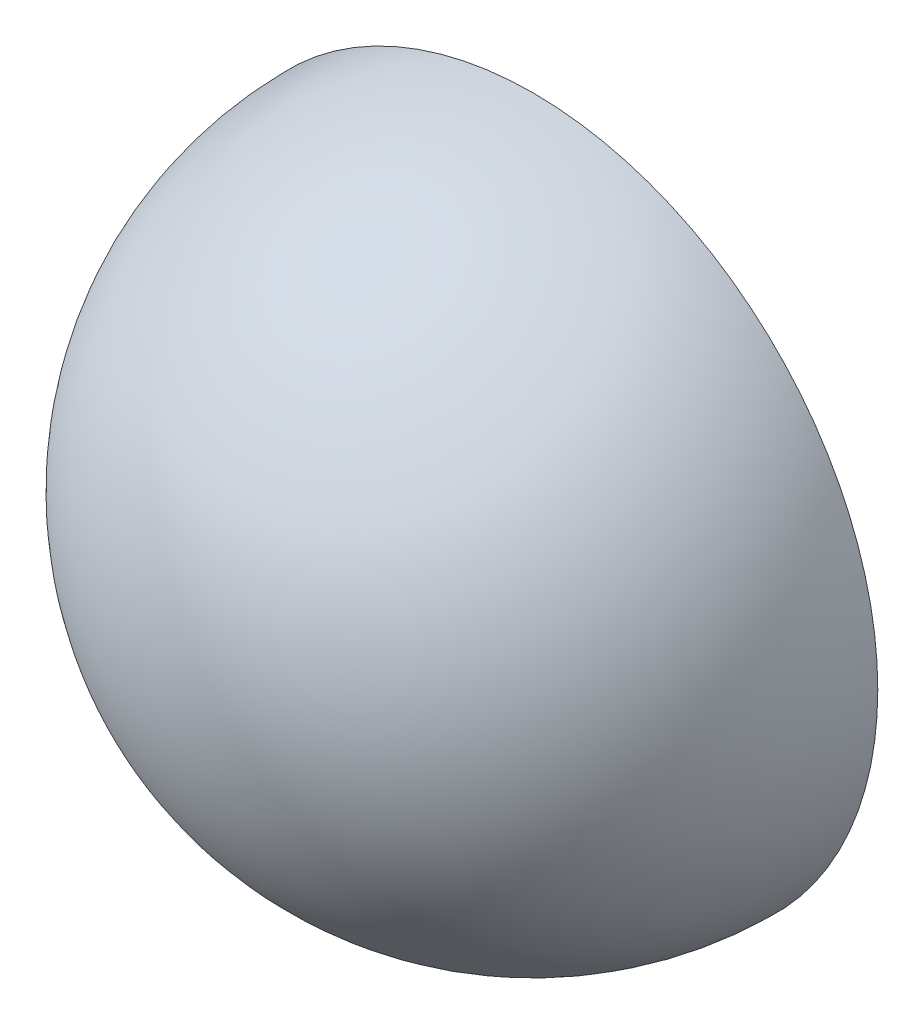
SolidWorks part; units mm, degrees
ref_plane "Front Plane" through (0, 0, 0) normal (0, 0, 1) x (1, 0, 0)
ref_plane "Top Plane" through (0, 0, 0) normal (0, 1, 0) x (1, 0, 0)
ref_plane "Right Plane" through (0, 0, 0) normal (1, 0, 0) x (0, 0, -1)
sketch "Sketch1" plane through (0, 0, 0) normal (0, 1, 0) x (1, 0, 0)
  line L0 (0, 0) -> (18.6879, 0) construction
  line L1 (0, 0) -> (0, -14.4281) construction
  line L2 (-2.5, 0) -> (0, 0)
  line L3 (0, -2.5) -> (0, 0)
  arc A0 (-2.5, 0) -> (0, -2.5) centre (0, 0) ccw
  dimension "D1" = 2.5
  dimension "D2" = 2.5
revolve "Revolve1" add sketch "Sketch1" angle 360 about L3
